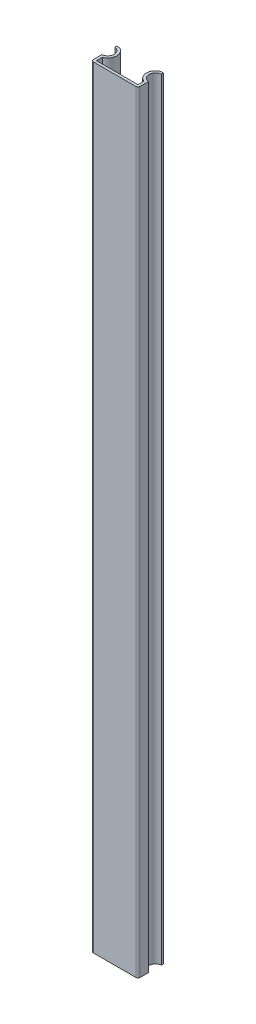
SolidWorks part; units mm, degrees
ref_plane "Face" through (0, 0, 0) normal (0, 0, 1) x (1, 0, 0)
ref_plane "Dessus" through (0, 0, 0) normal (0, 1, 0) x (1, 0, 0)
ref_plane "Droite" through (0, 0, 0) normal (1, 0, 0) x (0, 0, -1)
sketch "Esquisse1" plane through (0, 0, 0) normal (0, 1, 0) x (1, 0, 0)
  line L0 (5.5, 0) -> (-5.5, 0)
  line L1 (-5.5, 0) -> (-5.5, 2.4768)
  line L2 (0, 0) -> (0, 28.714) construction
  line L3 (4.9, 0.6) -> (-4.9, 0.6)
  line L4 (-4.9, 0.6) -> (-4.9, 2)
  line L5 (-5.5, 2.4768) -> (-5.5, 6) construction
  line L6 (-4.9, 2) -> (-4.9, 6) construction
  line L7 (-5.5, 6) -> (-5.5, 5.5232)
  line L8 (-5.5, 6) -> (-4.9, 6)
  line L9 (-3.5, 0) -> (-3.5, 8.1789) construction
  line L10 (5.5, 6) -> (5.5, 5.5232)
  line L11 (5.5, 6) -> (4.9, 6)
  line L12 (4.9, 0.6) -> (4.9, 2)
  line L13 (5.5, 0) -> (5.5, 2.4768)
  arc A0 (-4.9, 2) -> (-4.9, 6) centre (-5.6286, 4) ccw
  arc A1 (-5.5, 2.4768) -> (-5.5, 5.5232) centre (-5.6286, 4) ccw
  arc A2 (4.9, 2) -> (4.9, 6) centre (5.6286, 4) cw
  arc A3 (5.5, 2.4768) -> (5.5, 5.5232) centre (5.6286, 4) cw
  point P22 (0, 0.6)
  dimension "D6" = 0.6
  dimension "D1" = 0.6
  dimension "D2" = 0.6
  dimension "D3" = 5.5
  dimension "D4" = 2
  dimension "D5" = 6
  dimension "D7" = 3.5
extrude "Extrusion1" add sketch "Esquisse1" along normal blind 182
fillet "Congé1" radius 0.5 2 edges at (-5.5, 91, 0) (5.5, 91, 0)
